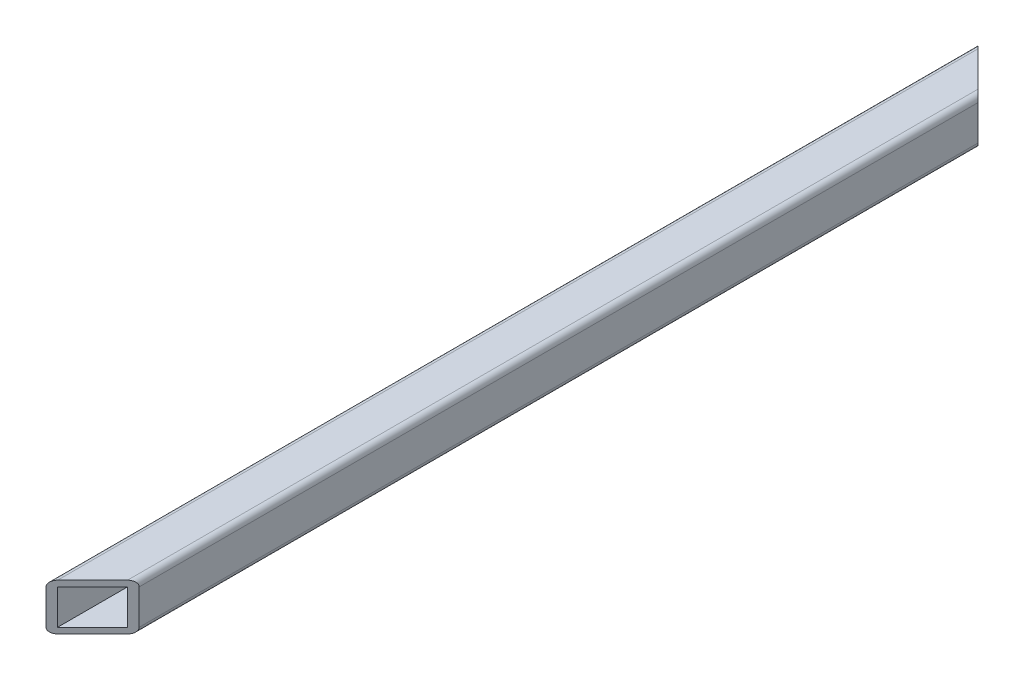
SolidWorks part; units mm, degrees
ref_plane "Front Plane" through (0, 0, 0) normal (0, 0, 1) x (1, 0, 0)
ref_plane "Top Plane" through (0, 0, 0) normal (0, 1, 0) x (1, 0, 0)
ref_plane "Right Plane" through (0, 0, 0) normal (1, 0, 0) x (0, 0, -1)
sketch "Sketch1" plane through (0, 0, 0) normal (0, 0, 1) x (1, 0, 0)
  line L1 (0, 0) -> (12.7, 0)
  line L2 (0, 0) -> (0, 12.7)
  line L3 (0, 12.7) -> (12.7, 12.7)
  line L4 (12.7, 0) -> (12.7, 12.7)
  line L5 (11.1125, 11.1125) -> (1.5875, 11.1125)
  line L6 (11.1125, 11.1125) -> (11.1125, 1.5875)
  line L7 (11.1125, 1.5875) -> (1.5875, 1.5875)
  line L8 (1.5875, 11.1125) -> (1.5875, 1.5875)
  dimension "D1" = 12.7
  dimension "D2" = 1.5875
  dimension "D3" = 1.5875
  dimension "D4" = 1.5875
extrude "Boss-Extrude1" add sketch "Sketch1" along normal blind 254
sketch "Sketch2" plane through (0, 12.7, 0) normal (0, 1, 0) x (1, 0, 0)
  line L0 (0, -254) -> (12.7, -254)
  line L1 (12.7, -254) -> (12.7, -241.3)
  line L2 (12.7, -254) -> (12.7, 0) construction
  line L3 (12.7, -241.3) -> (0, -254)
  line L4 (0, 0) -> (12.7, -12.7)
  line L5 (12.7, -12.7) -> (12.7, 0)
  line L6 (12.7, 0) -> (0, 0)
extrude "Cut-Extrude1" cut sketch "Sketch2" against normal through all
fillet "Fillet1" radius 1.5875 4 edges at (12.7, 0, 127) (0, 0, 127) (0, 12.7, 127) (12.7, 12.7, 127)
sketch "Sketch3" plane through (0, 0, 0) normal (-1, 0, 0) x (0, 0, 1)
  line L0 (136.525, 6.35) -> (117.475, 6.35) construction
  line L1 (254, 11.1125) -> (0, 11.1125) construction
  line L2 (254, 11.1125) -> (254, 1.5875) construction
  circle A0 centre (136.525, 6.35) radius 2.032
  circle A1 centre (117.475, 6.35) radius 2.032
  point P6 (127, 11.1125)
  point P7 (127, 6.35)
  point P10 (254, 6.35)
  dimension "D1" = 4.064
  dimension "D2" = 19.05
extrude "Cut-Extrude2" cut sketch "Sketch3" against normal up to next
